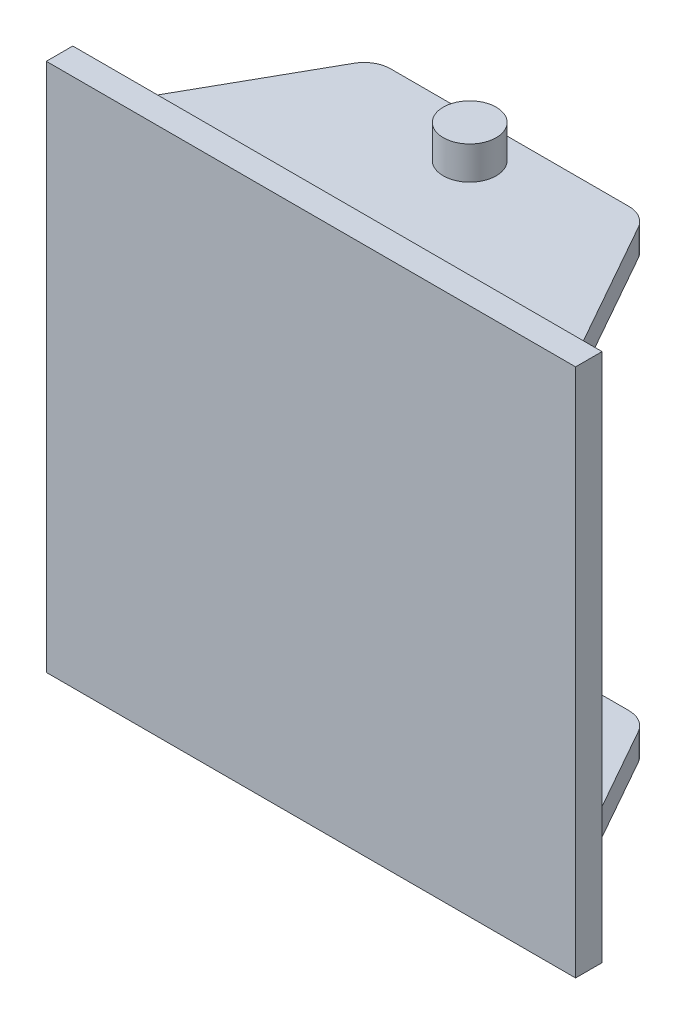
SolidWorks part; units mm, degrees
ref_plane "Front Plane" through (0, 0, 0) normal (0, 0, 1) x (1, 0, 0)
ref_plane "Top Plane" through (0, 0, 0) normal (0, 1, 0) x (1, 0, 0)
ref_plane "Right Plane" through (0, 0, 0) normal (1, 0, 0) x (0, 0, -1)
sketch "Sketch1" plane through (0, 0, 0) normal (0, 0, 1) x (1, 0, 0)
  line L1 (100, 100) -> (-100, 100)
  line L2 (100, 100) -> (100, -100)
  line L3 (100, -100) -> (-100, -100)
  line L4 (-100, 100) -> (-100, -100)
  line L5 (100, 100) -> (-100, -100) construction
  line L6 (100, -100) -> (-100, 100) construction
  point P0 (0, 0)
  dimension "D1" = 200
extrude "Boss-Extrude1" add sketch "Sketch1" along normal blind 10
sketch "Sketch2" plane through (0, 0, 0) normal (0, 0, -1) x (-1, 0, 0)
  line L1 (87.5, 87.5) -> (-87.5, 87.5)
  line L2 (87.5, 87.5) -> (87.5, -87.5)
  line L3 (87.5, -87.5) -> (-87.5, -87.5)
  line L4 (-87.5, 87.5) -> (-87.5, -87.5)
  line L5 (87.5, 87.5) -> (-87.5, -87.5) construction
  line L6 (87.5, -87.5) -> (-87.5, 87.5) construction
  point P0 (0, 0)
  dimension "D1" = 175
extrude "Boss-Extrude2" add sketch "Sketch2" along normal blind 75
sketch "Sketch5" plane through (0, 87.5, 0) normal (0, 1, 0) x (1, 0, 0)
  line L0 (-87.5, 0) -> (-53.7135, 60)
  line L1 (-45, 65.0934) -> (45, 65.0934)
  line L2 (0, 0) -> (0, 56.3458) construction
  line L3 (-87.5, 0) -> (87.5, 0) construction
  line L4 (87.5, 0) -> (53.7135, 60)
  line L5 (87.5, 75) -> (87.5, 0) construction
  line L6 (-87.5, 75) -> (87.5, 75) construction
  line L7 (-87.5, 75) -> (-87.5, 0) construction
  line L8 (87.5, 75) -> (87.5, 0)
  line L9 (-87.5, 75) -> (87.5, 75)
  line L10 (-87.5, 75) -> (-87.5, 0)
  arc A0 (-45, 65.0934) -> (-53.7135, 60) centre (-45, 55.0934) ccw
  arc A1 (45, 65.0934) -> (53.7135, 60) centre (45, 55.0934) cw
  point P8 (0, 65.0934)
  dimension "D1" = 20
  dimension "D2" = 60
  dimension "D3" = 45
extrude "Cut-Extrude2" cut sketch "Sketch5" against normal through all
sketch "Sketch6" plane through (0, 0, 0) normal (1, 0, 0) x (0, 0, -1)
  line L0 (65.0934, -87.5) -> (65.0934, 87.5) construction
  line L1 (65.0934, 77.5) -> (15, 77.5)
  line L2 (65.0934, 77.5) -> (65.0934, -77.5)
  line L3 (65.0934, -77.5) -> (15, -77.5)
  line L4 (15, 77.5) -> (15, -77.5)
  line L5 (60, 87.5) -> (0, 87.5) construction
  line L6 (60, -87.5) -> (0, -87.5) construction
  line L7 (0, -100) -> (0, 100) construction
  dimension "D1" = 10
  dimension "D2" = 10
  dimension "D3" = 15
extrude "Cut-Extrude3" cut sketch "Sketch6" against normal mid plane 200
sketch "Sketch7" plane through (0, 0, 0) normal (0, 1, 0) x (1, 0, 0)
  circle A0 centre (0, 50) radius 10
  dimension "D1" = 20
  dimension "D2" = 50
extrude "Boss-Extrude4" add sketch "Sketch7" along normal mid plane 200
